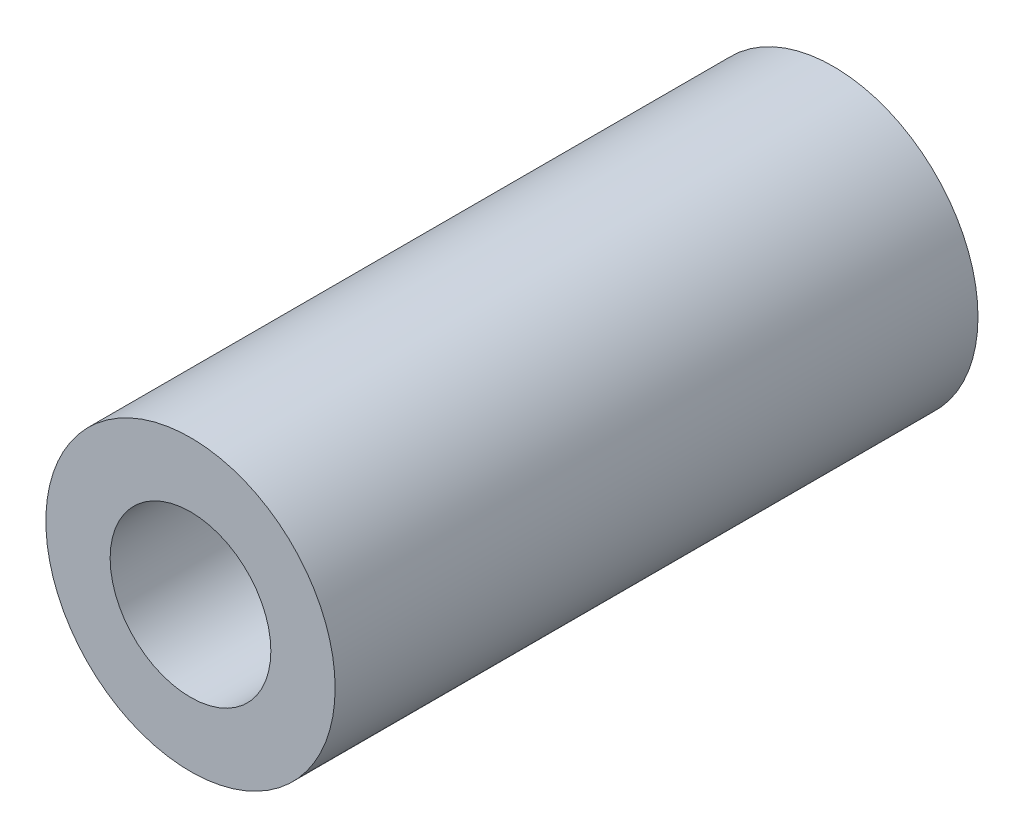
SolidWorks part; units mm, degrees
material "PBT Uniwersalny"
ref_plane "Płaszczyzna przednia" through (0, 0, 0) normal (0, 0, 1) x (1, 0, 0)
ref_plane "Płaszczyzna górna" through (0, 0, 0) normal (0, 1, 0) x (1, 0, 0)
ref_plane "Płaszczyzna prawa" through (0, 0, 0) normal (1, 0, 0) x (0, 0, -1)
sketch "Szkic1" plane through (0, 0, 0) normal (0, 0, 1) x (1, 0, 0)
  circle A1 centre (0, 0) radius 1.75
  circle A2 centre (0, 0) radius 3.15
  dimension "D2" = 3.5
  dimension "D1" = 6.3
extrude "Dodanie-wyciągnięcie1" add sketch "Szkic1" along normal blind 14
